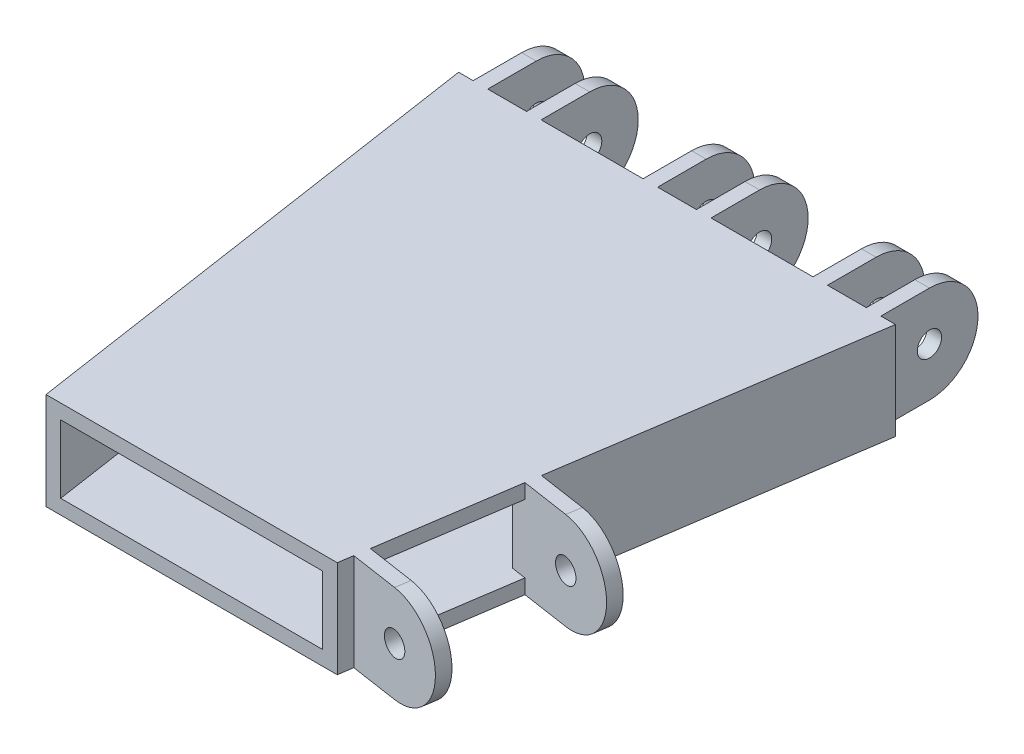
SolidWorks part; units mm, degrees
ref_plane "Front Plane" through (0, 0, 0) normal (0, 0, 1) x (1, 0, 0)
ref_plane "Top Plane" through (0, 0, 0) normal (0, 1, 0) x (1, 0, 0)
ref_plane "Right Plane" through (0, 0, 0) normal (1, 0, 0) x (0, 0, -1)
sketch "Sketch1" plane through (0, 0, 0) normal (0, 1, 0) x (1, 0, 0)
  line L0 (-45, 0) -> (45, 0)
  line L1 (45, 0) -> (30, -100)
  line L2 (30, -100) -> (-30, -100)
  line L3 (-30, -100) -> (-45, 0)
  point P2 (0, 0)
  dimension "D1" = 60
  dimension "D3" = 90
  dimension "D4" = 100
extrude "Boss-Extrude1" add sketch "Sketch1" along normal mid plane 20
sketch "Sketch2" plane through (0, 0, 0) normal (1, 0, 0) x (0, 0, -1)
  line L0 (0, 10) -> (0, -10) construction
  line L1 (0, -10) -> (-100, -10) construction
  line L2 (0, 10) -> (0, -10) construction
  line L3 (0, -10) -> (-100, -10) construction
  line L5 (0, 10) -> (10, 10)
  line L6 (0, 10) -> (0, -10)
  line L7 (0, -10) -> (10, -10)
  arc A0 (10, -10) -> (10, 10) centre (10, 0) ccw
  circle A1 centre (10, 0) radius 2.5
  dimension "D2" = 10
  dimension "D3" = 5
  dimension "D1" = 10
extrude "Boss-Extrude2" add sketch "Sketch2" along normal mid plane 14 from offset 35
pattern_linear "LPattern1" count 3 spacing 35 along (-1, 0, 0) of "Boss-Extrude2"
shell "Shell1" thickness 3
sketch "Sketch3" plane through (0, 0, 0) normal (0, 0, 1) x (1, 0, 0)
  line L0 (-42, 10) -> (-42, -10) construction
  line L1 (-42, -10) -> (-45, -10) construction
  line L2 (-45, -10) -> (-45, 10) construction
  line L3 (-45, 10) -> (-42, 10) construction
  line L4 (42, -10) -> (42, 10) construction
  line L5 (42, 10) -> (45, 10) construction
  line L6 (45, 10) -> (45, -10) construction
  line L7 (45, -10) -> (42, -10) construction
  line L8 (28, -10) -> (7, -10) construction
  line L9 (28, 10) -> (7, 10) construction
  line L10 (-7, 10) -> (-28, 10) construction
  line L11 (-7, -10) -> (-28, -10) construction
  line L12 (-45, 10) -> (-45, -10) construction
  line L13 (-42, 10) -> (-45, 10) construction
  line L14 (45, 10) -> (42, 10) construction
  line L15 (-42, 10) -> (-42, -10) construction
  line L16 (-42, -10) -> (-45, -10) construction
  line L17 (-45, -10) -> (-45, 10) construction
  line L18 (-45, 10) -> (-42, 10) construction
  line L19 (42, -10) -> (42, 10) construction
  line L20 (42, 10) -> (45, 10) construction
  line L21 (45, 10) -> (45, -10) construction
  line L22 (45, -10) -> (42, -10) construction
  line L23 (28, -10) -> (7, -10) construction
  line L24 (28, 10) -> (7, 10) construction
  line L25 (-7, 10) -> (-28, 10) construction
  line L26 (-7, -10) -> (-28, -10) construction
  line L27 (-45, 10) -> (-45, -10) construction
  line L28 (-42, 10) -> (-45, 10) construction
  line L29 (45, 10) -> (42, 10) construction
  line L31 (42, 10) -> (28, 10) construction
  line L32 (42, 10) -> (42, -10) construction
  line L33 (42, -10) -> (28, -10) construction
  line L34 (28, 10) -> (28, -10) construction
  line L35 (7, 10) -> (-7, 10) construction
  line L36 (7, 10) -> (7, -10) construction
  line L37 (7, -10) -> (-7, -10) construction
  line L38 (-7, 10) -> (-7, -10) construction
  line L39 (-28, 10) -> (-42, 10) construction
  line L40 (-28, 10) -> (-28, -10) construction
  line L41 (-28, -10) -> (-42, -10) construction
  line L42 (-42, 10) -> (-42, -10) construction
  line L43 (39, 10) -> (31, 10)
  line L44 (39, 10) -> (39, -10)
  line L45 (39, -10) -> (31, -10)
  line L46 (31, 10) -> (31, -10)
  line L47 (4, 10) -> (-4, 10)
  line L48 (4, 10) -> (4, -10)
  line L49 (4, -10) -> (-4, -10)
  line L50 (-4, 10) -> (-4, -10)
  line L51 (-31, 10) -> (-39, 10)
  line L52 (-31, 10) -> (-31, -10)
  line L53 (-31, -10) -> (-39, -10)
  line L54 (-39, 10) -> (-39, -10)
  dimension "D1" = 3
  dimension "D2" = 3
  dimension "D3" = 3
  dimension "D4" = 3
  dimension "D5" = 3
  dimension "D6" = 3
extrude "Cut-Extrude1" cut sketch "Sketch3" against normal blind 20
ref_plane "thumb plane" through (-14.0098, 0, 93.3985) normal (-0.1483, 0, 0.9889) x (0.9889, 0, 0.1483)
sketch "Sketch5" plane through (-14.0098, 0, 93.3985) normal (-0.1483, 0, 0.9889) x (0.9889, 0, 0.1483)
  line L0 (44.5021, 10) -> (44.5021, -10) construction
  line L1 (44.5021, 10) -> (44.5021, -10) construction
  line L3 (44.5021, 10) -> (54.5021, 10)
  line L4 (44.5021, 10) -> (44.5021, -10)
  line L5 (44.5021, -10) -> (54.5021, -10)
  arc A0 (54.5021, -10) -> (54.5021, 10) centre (54.5021, 0) ccw
  circle A1 centre (54.5021, 0) radius 2.5
  dimension "D2" = 5
  dimension "D1" = 10
extrude "Boss-Extrude3" add sketch "Sketch5" against normal blind 3 from offset 3 offset against normal yes
pattern_linear "LPattern2" count 2 spacing 31 along (0.1483, 0, -0.9889) of "Boss-Extrude3"
sketch "Sketch6" plane through (44.0098, 0, 6.6015) normal (0.9889, 0, 0.1483) x (0.1483, 0, -0.9889)
  line L0 (-88.4434, 10) -> (-88.4434, -10) construction
  line L1 (-88.4434, 7) -> (-60.4434, 7)
  line L2 (-88.4434, 7) -> (-88.4434, -7)
  line L3 (-88.4434, -7) -> (-60.4434, -7)
  line L4 (-60.4434, 7) -> (-60.4434, -7)
  line L5 (-60.4434, 10) -> (-60.4434, -10) construction
  line L6 (-88.4434, 10) -> (-60.4434, 10) construction
  line L7 (-88.4434, -10) -> (-60.4434, -10) construction
  dimension "D1" = 3
  dimension "D2" = 3
extrude "Cut-Extrude2" cut sketch "Sketch6" against normal blind 3
